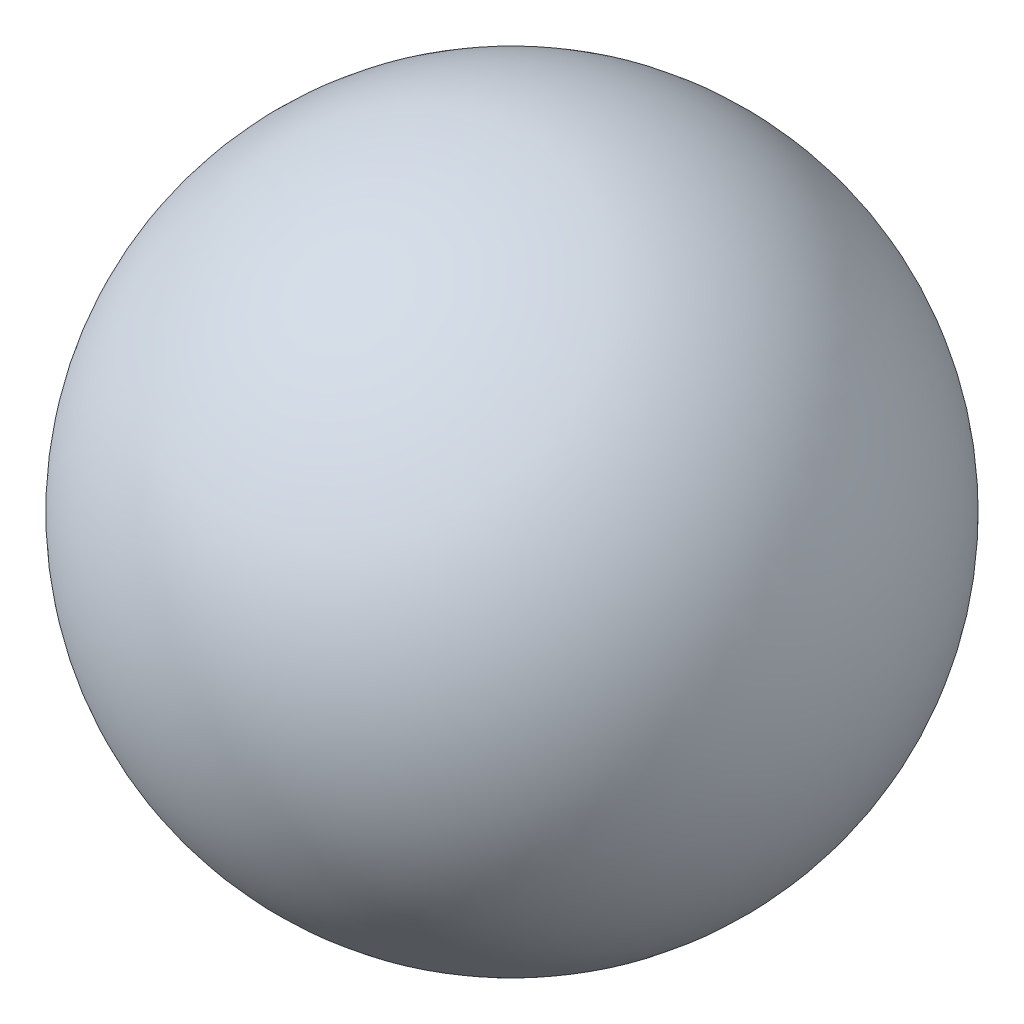
SolidWorks part; units mm, degrees
ref_plane "Ebene vorne" through (0, 0, 0) normal (0, 0, 1) x (1, 0, 0)
ref_plane "Ebene oben" through (0, 0, 0) normal (0, 1, 0) x (1, 0, 0)
ref_plane "Ebene rechts" through (0, 0, 0) normal (1, 0, 0) x (0, 0, -1)
sketch "Skizze1" plane through (0, 0, 0) normal (0, 0, 1) x (1, 0, 0)
  line L1 (0, 0) -> (0, 25)
  line L2 (0, 0) -> (0, -25)
  arc A0 (0, -25) -> (0, 25) centre (0, 0) cw
  dimension "D1" = 50
revolve "Rotation1" add sketch "Skizze1" angle 360 about L1
